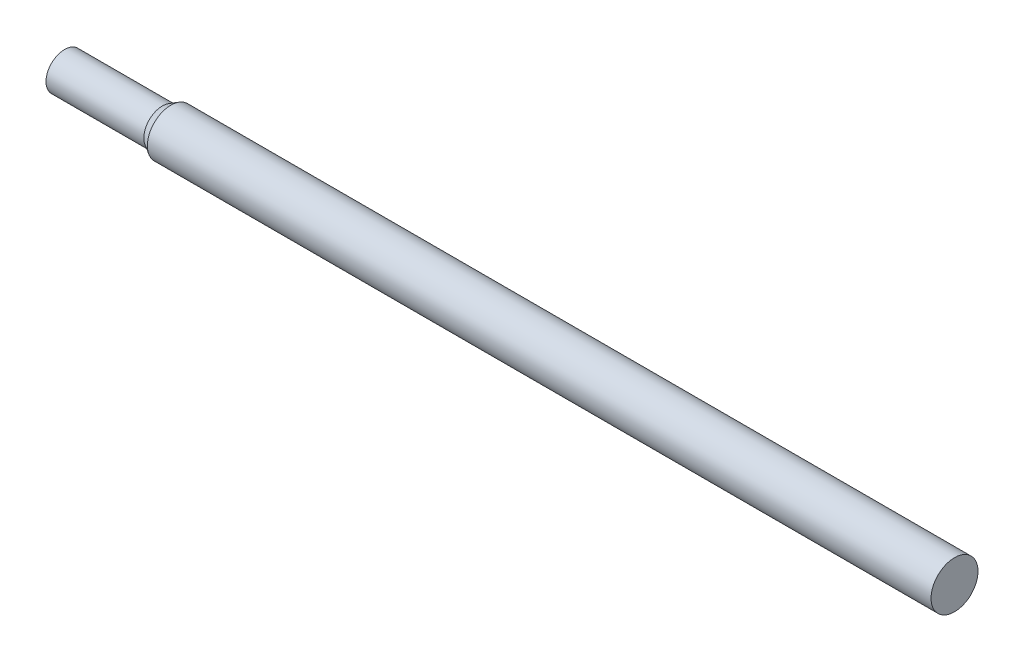
SolidWorks part; units mm, degrees
ref_plane "前视基准面" through (0, 0, 0) normal (0, 0, 1) x (1, 0, 0)
ref_plane "上视基准面" through (0, 0, 0) normal (0, 1, 0) x (1, 0, 0)
ref_plane "右视基准面" through (0, 0, 0) normal (1, 0, 0) x (0, 0, -1)
sketch "草图3" plane through (0, 0, 0) normal (1, 0, 0) x (0, 0, -1)
  circle A0 centre (0, 0) radius 24
  dimension "D1" = 48
extrude "凸台-拉伸2" add sketch "草图3" along normal blind 910
sketch "草图4" plane through (0, 0, 0) normal (0, 1, 0) x (1, 0, 0)
  line L0 (0, 24) -> (0, 19)
  line L1 (0, 24) -> (0, -24) construction
  line L2 (0, 19) -> (100, 19)
  line L3 (100, 19) -> (108.6603, 24)
  line L4 (910, 24) -> (0, 24) construction
  line L5 (108.6603, 24) -> (0, 24)
  line L6 (0, 0) -> (80.9422, 0) construction
  dimension "D1" = 100
  dimension "D2" = 30
  dimension "D3" = 5
revolve "切除-旋转1" cut sketch "草图4" angle 360 about L6
sketch "草图5" plane through (0, 0, 0) normal (-1, 0, 0) x (0, 0, 1)
  line L1 (3, 23.8118) -> (3, 18.7617)
  line L2 (-3, 23.8118) -> (-3, 18.7617)
  arc A0 (3, 18.7617) -> (-3, 18.7617) centre (0, 0) ccw
  arc A1 (3, 23.8118) -> (-3, 23.8118) centre (0, 0) ccw
